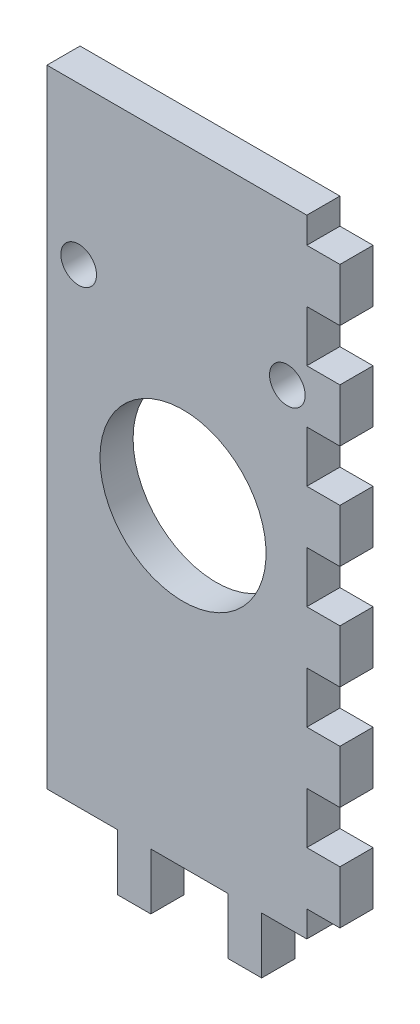
SolidWorks part; units mm, degrees
ref_plane "Front Plane" through (0, 0, 0) normal (0, 0, 1) x (1, 0, 0)
ref_plane "Top Plane" through (0, 0, 0) normal (0, 1, 0) x (1, 0, 0)
ref_plane "Right Plane" through (0, 0, 0) normal (1, 0, 0) x (0, 0, -1)
sketch "Sketch1" plane through (0, 0, 0) normal (0, 1, 0) x (1, 0, 0)
  line L0 (0, 0) -> (-50.5, 0) construction
  line L1 (0, 0) -> (0, 50.5) construction
  line L2 (-50.5, 22.5) -> (-22.5, 22.5)
  line L3 (-22.5, 22.5) -> (-22.5, 50.5)
  line L5 (-22.5, 22.5) -> (-50.5, 22.5)
  line L6 (-22.5, 22.5) -> (-22.5, 25.675)
  line L7 (-22.5, 25.675) -> (-50.5, 25.675)
  line L8 (-50.5, 22.5) -> (-50.5, 25.675)
  line L9 (-22.5, 22.5) -> (-25.675, 22.5)
  line L10 (-22.5, 22.5) -> (-22.5, 50.5)
  line L11 (-22.5, 50.5) -> (-25.675, 50.5)
  line L12 (-25.675, 22.5) -> (-25.675, 50.5)
  point P7 (-37.5, 22.5)
  point P8 (-22.5, 37.5)
  dimension "D1" = 50.5
  dimension "D2" = 50.5
  dimension "D3" = 22.5
  dimension "D4" = 22.5
  dimension "D5" = 37.5
  dimension "D6" = 37.5
  dimension "D7" = 28
  dimension "D8" = 28
  dimension "D9" = 3.175
  dimension "D10" = 3.175
extrude "Boss-Extrude1" add sketch "Sketch1" along normal blind 60 contours L2 L12 L7 L8 | L12 L5 L3 L7 | L12 L7 L3 L11
sketch "Sketch2" plane through (0, 0, -22.5) normal (0, 0, 1) x (1, 0, 0)
  line L0 (-50.5, 30) -> (-22.5, 30) construction
  line L1 (-50.5, 60) -> (-50.5, 0) construction
  line L2 (-22.5, 60) -> (-22.5, 0) construction
  line L3 (-37.5, 60) -> (-37.5, 0) construction
  line L4 (-50.5, 60) -> (-22.5, 60) construction
  line L5 (-50.5, 0) -> (-22.5, 0) construction
  line L7 (-50.5, 60) -> (-22.5758, 60)
  line L15 (-33.125, -5.4) -> (-33.125, 0)
  line L16 (-30, -5.4) -> (-33.125, -5.4)
  line L17 (-30, -5.4) -> (-30, 0)
  line L18 (-40.625, -5.4) -> (-40.625, 0)
  line L19 (-43.75, -5.4) -> (-40.625, -5.4)
  line L20 (-43.75, -5.4) -> (-43.75, 0)
  circle A0 centre (-37.5, 30) radius 8
  dimension "D2" = 16
  dimension "D1" = 15
  dimension "D3" = 5.4
  dimension "D4" = 7.5
  dimension "D6" = 3.125
  dimension "D5" = 7.5
sketch "Sketch3" plane through (-22.5, 0, 0) normal (1, 0, 0) x (0, 0, -1)
  line L0 (22.5, 30) -> (50.5, 30) construction
  line L1 (22.5, 60) -> (22.5, 0) construction
  line L2 (50.5, 60) -> (50.5, 0) construction
  line L3 (37.5, 60) -> (37.5, 0) construction
  line L4 (22.5, 60) -> (50.5, 60) construction
  line L5 (22.5, 0) -> (50.5, 0) construction
  circle A0 centre (37.5, 30) radius 8
  dimension "D1" = 16
  dimension "D2" = 15
extrude "Boss-Extrude4" add sketch "Sketch2" against normal blind 3.175
sketch "Sketch4" plane through (0, 0, -22.5) normal (0, 0, 1) x (1, 0, 0)
  line L0 (-50.5, 30) -> (-22.5, 30) construction
  line L1 (-50.5, 60) -> (-50.5, 0) construction
  line L2 (-22.5, 22) -> (-22.5, 38) construction
  line L3 (-37.5, 60) -> (-37.5, 0) construction
  line L4 (-50.5, 60) -> (-22.5, 60) construction
  line L5 (-50.5, 0) -> (-43.75, 0) construction
  line L6 (-22.5, 60) -> (-22.5, 0) construction
  circle A0 centre (-37.5, 30) radius 8
  dimension "D1" = 16
  dimension "D2" = 15
extrude "Cut-Extrude1" cut sketch "Sketch4" against normal blind 3.175
extrude "Cut-Extrude2" cut sketch "Sketch3" against normal blind 3.175
sketch "Sketch5" plane through (-22.5, 0, 0) normal (1, 0, 0) x (0, 0, -1)
  line L0 (22.5, 0) -> (50.5, 0) construction
  line L1 (22.5, 60) -> (50.5, 60)
  line L10 (22.5, 30) -> (50.5, 30) construction
  line L11 (22.5, 60) -> (22.5, 0) construction
  line L12 (50.5, 60) -> (50.5, 0) construction
  line L13 (43.85, -5.4) -> (43.85, 0)
  line L14 (40.675, -5.4) -> (43.85, -5.4)
  line L15 (40.675, -5.4) -> (40.675, 0)
  line L16 (33.175, -5.4) -> (33.175, 0)
  line L17 (30, -5.4) -> (33.175, -5.4)
  line L18 (30, -5.4) -> (30, 0)
  line L19 (30, 0) -> (33.175, 0)
  line L28 (40.675, 0) -> (43.85, 0)
  point P7 (37.5, 30)
  point P8 (-4.2304, -0.8722)
  point P10 (8.5502, 17.2274)
  dimension "D1" = 7.5
  dimension "D2" = 5.4
  dimension "D3" = 3.175
  dimension "D4" = 7.5
extrude "Boss-Extrude5" add sketch "Sketch5" against normal blind 3.175
sketch "Sketch6" plane through (0, 0, -22.5) normal (0, 0, 1) x (1, 0, 0)
  line L0 (-50.5, 45) -> (-22.5, 45) construction
  line L1 (-50.5, 60) -> (-50.5, 0) construction
  line L2 (-22.5, 60) -> (-22.5, 0) construction
  line L3 (-37.5, 60) -> (-37.5, 0) construction
  line L4 (-50.5, 60) -> (-22.5, 60) construction
  line L5 (-40.625, 0) -> (-33.125, 0) construction
  circle A0 centre (-37.5, 30) radius 8 construction
  circle A1 centre (-37.5, 30) radius 8 construction
  circle A2 centre (-47.5, 45) radius 1.75
  circle A3 centre (-27.5, 45) radius 1.75
  dimension "D1" = 15
  dimension "D3" = 3.5
  dimension "D2" = 10
extrude "Cut-Extrude3" cut sketch "Sketch6" against normal blind 10 contours A2 | A3
sketch "Sketch7" plane through (-22.5, 0, 0) normal (1, 0, 0) x (0, 0, -1)
  line L0 (37.5, 60) -> (37.5, 0) construction
  line L1 (22.5, 60) -> (50.5, 60) construction
  line L2 (33.175, 0) -> (40.675, 0) construction
  line L4 (22.5, 60) -> (22.5, 0) construction
  line L5 (22.5, 45) -> (50.5, 45) construction
  line L6 (50.5, 60) -> (50.5, 0) construction
  circle A0 centre (37.5, 30) radius 8 construction
  circle A1 centre (37.5, 30) radius 8 construction
  circle A2 centre (47.5, 45) radius 1.75
  circle A3 centre (27.5, 45) radius 1.75
  dimension "D1" = 15
  dimension "D3" = 3.5
  dimension "D2" = 10
extrude "Cut-Extrude4" cut sketch "Sketch7" against normal blind 10
sketch "Sketch8" plane through (0, 0, -50.5) normal (0, 0, -1) x (-1, 0, 0)
  line L1 (22.5, 60) -> (25.675, 60)
  line L2 (22.5, 60) -> (22.5, -5.4)
  line L3 (22.5, -5.4) -> (25.675, -5.4)
  line L4 (25.675, 60) -> (25.675, -5.4)
extrude "Cut-Extrude6" cut sketch "Sketch8" against normal up to surface (24.825 mm away) up to face at (-37.2792, 8.2, -25.675)
sketch "Sketch9" plane through (0, 0, -25.675) normal (0, 0, -1) x (-1, 0, 0)
  line L0 (22.5, 60) -> (22.5, 0) construction
  line L1 (22.5, 57.5) -> (25.675, 57.5)
  line L2 (22.5, 57.5) -> (22.5, 52.5)
  line L3 (22.5, 52.5) -> (25.675, 52.5)
  line L4 (25.675, 57.5) -> (25.675, 52.5)
  line L5 (25.675, 60) -> (25.675, 0)
  line L6 (22.5, 60) -> (50.5, 60) construction
  line L7 (22.5, 0) -> (30, 0) construction
  line L8 (22.5, 47.5) -> (25.675, 47.5)
  line L9 (22.5, 42.5) -> (25.675, 42.5)
  line L10 (25.675, 47.5) -> (25.675, 42.5)
  line L11 (22.5, 47.5) -> (22.5, 42.5)
  line L12 (22.5, 37.5) -> (25.675, 37.5)
  line L13 (22.5, 32.5) -> (25.675, 32.5)
  line L14 (25.675, 37.5) -> (25.675, 32.5)
  line L15 (22.5, 37.5) -> (22.5, 32.5)
  line L16 (22.5, 27.5) -> (25.675, 27.5)
  line L17 (22.5, 22.5) -> (25.675, 22.5)
  line L18 (25.675, 27.5) -> (25.675, 22.5)
  line L19 (22.5, 27.5) -> (22.5, 22.5)
  line L20 (22.5, 17.5) -> (25.675, 17.5)
  line L21 (22.5, 12.5) -> (25.675, 12.5)
  line L22 (25.675, 17.5) -> (25.675, 12.5)
  line L23 (22.5, 17.5) -> (22.5, 12.5)
  line L24 (22.5, 7.5) -> (25.675, 7.5)
  line L25 (22.5, 2.5) -> (25.675, 2.5)
  line L26 (25.675, 7.5) -> (25.675, 2.5)
  line L27 (22.5, 7.5) -> (22.5, 2.5)
  line M6 (22.5, 0) -> (30, 0)
  line M16 (50.5, 60) -> (22.5, 60)
  line M17 (22.5, 60) -> (22.5, 0)
  dimension "D2" = 5
  dimension "D3" = 2.5
  dimension "D4" = 5
  dimension "D5" = 3.175
  dimension "D1" = 6
extrude "Cut-Extrude8" cut sketch "Sketch9" against normal blind 10 contours L5 L1 M16 M17 | L8 L5 L3 M17 | L12 L5 L9 M17 | L16 L5 L13 M17 | L20 L5 L17 M17 | L24 L5 L21 M17 | L25 L5 M17 M6
sketch "Sketch10" plane through (0, 0, -25.675) normal (0, 0, -1) x (-1, 0, 0)
  line L108 (25.6344, 60.0406) -> (25.6344, 57.5406)
  line L109 (25.6344, 57.5406) -> (22.4594, 57.5406)
  line L110 (22.4594, 57.5406) -> (22.4594, 52.4594)
  line L111 (22.4594, 52.4594) -> (25.6344, 52.4594)
  line L112 (25.6344, 52.4594) -> (25.6344, 47.5406)
  line L113 (25.6344, 47.5406) -> (22.4594, 47.5406)
  line L114 (22.4594, 47.5406) -> (22.4594, 42.4594)
  line L115 (22.4594, 42.4594) -> (25.6344, 42.4594)
  line L116 (25.6344, 42.4594) -> (25.6344, 37.5406)
  line L117 (25.6344, 37.5406) -> (22.4594, 37.5406)
  line L118 (22.4594, 37.5406) -> (22.4594, 32.4594)
  line L119 (22.4594, 32.4594) -> (25.6344, 32.4594)
  line L120 (25.6344, 32.4594) -> (25.6344, 27.5406)
  line L121 (25.6344, 27.5406) -> (22.4594, 27.5406)
  line L122 (22.4594, 27.5406) -> (22.4594, 22.4594)
  line L123 (22.4594, 22.4594) -> (25.6344, 22.4594)
  line L124 (25.6344, 22.4594) -> (25.6344, 17.5406)
  line L125 (25.6344, 17.5406) -> (22.4594, 17.5406)
  line L126 (22.4594, 17.5406) -> (22.4594, 12.4594)
  line L127 (22.4594, 12.4594) -> (25.6344, 12.4594)
  line L128 (25.6344, 12.4594) -> (25.6344, 7.5406)
  line L129 (25.6344, 7.5406) -> (22.4594, 7.5406)
  line L130 (22.4594, 7.5406) -> (22.4594, 2.4594)
  line L131 (22.4594, 2.4594) -> (25.6344, 2.4594)
  line L132 (25.6344, 2.4594) -> (25.6344, -0.0406)
  line L133 (25.6344, -0.0406) -> (29.9594, -0.0406)
  line L134 (29.9594, -0.0406) -> (29.9594, -5.4406)
  line L135 (29.9594, -5.4406) -> (33.1656, -5.4406)
  line L136 (33.1656, -5.4406) -> (33.1656, -0.0406)
  line L137 (33.1656, -0.0406) -> (40.5844, -0.0406)
  line L138 (40.5844, -0.0406) -> (40.5844, -5.4406)
  line L139 (40.5844, -5.4406) -> (43.7906, -5.4406)
  line L140 (43.7906, -5.4406) -> (43.7906, -0.0406)
  line L141 (43.7906, -0.0406) -> (50.5406, -0.0406)
  line L142 (50.5406, -0.0406) -> (50.5406, 60.0406)
  line L143 (50.5406, 60.0406) -> (25.6344, 60.0406)
  line L144 (25.6344, 60.0406) -> (25.6344, 57.5406)
  line L145 (25.6344, 57.5406) -> (22.4594, 57.5406)
  line L146 (22.4594, 57.5406) -> (22.4594, 52.4594)
  line L147 (22.4594, 52.4594) -> (25.6344, 52.4594)
  line L148 (25.6344, 52.4594) -> (25.6344, 47.5406)
  line L149 (25.6344, 47.5406) -> (22.4594, 47.5406)
  line L150 (22.4594, 47.5406) -> (22.4594, 42.4594)
  line L151 (22.4594, 42.4594) -> (25.6344, 42.4594)
  line L152 (25.6344, 42.4594) -> (25.6344, 37.5406)
  line L153 (25.6344, 37.5406) -> (22.4594, 37.5406)
  line L154 (22.4594, 37.5406) -> (22.4594, 32.4594)
  line L155 (22.4594, 32.4594) -> (25.6344, 32.4594)
  line L156 (25.6344, 32.4594) -> (25.6344, 27.5406)
  line L157 (25.6344, 27.5406) -> (22.4594, 27.5406)
  line L158 (22.4594, 27.5406) -> (22.4594, 22.4594)
  line L159 (22.4594, 22.4594) -> (25.6344, 22.4594)
  line L160 (25.6344, 22.4594) -> (25.6344, 17.5406)
  line L161 (25.6344, 17.5406) -> (22.4594, 17.5406)
  line L162 (22.4594, 17.5406) -> (22.4594, 12.4594)
  line L163 (22.4594, 12.4594) -> (25.6344, 12.4594)
  line L164 (25.6344, 12.4594) -> (25.6344, 7.5406)
  line L165 (25.6344, 7.5406) -> (22.4594, 7.5406)
  line L166 (22.4594, 7.5406) -> (22.4594, 2.4594)
  line L167 (22.4594, 2.4594) -> (25.6344, 2.4594)
  line L168 (25.6344, 2.4594) -> (25.6344, -0.0406)
  line L169 (25.6344, -0.0406) -> (29.9594, -0.0406)
  line L170 (29.9594, -0.0406) -> (29.9594, -5.4406)
  line L171 (29.9594, -5.4406) -> (33.1656, -5.4406)
  line L172 (33.1656, -5.4406) -> (33.1656, -0.0406)
  line L173 (33.1656, -0.0406) -> (40.5844, -0.0406)
  line L174 (40.5844, -0.0406) -> (40.5844, -5.4406)
  line L175 (40.5844, -5.4406) -> (43.7906, -5.4406)
  line L176 (43.7906, -5.4406) -> (43.7906, -0.0406)
  line L177 (43.7906, -0.0406) -> (50.5406, -0.0406)
  line L178 (50.5406, -0.0406) -> (50.5406, 60.0406)
  line L179 (50.5406, 60.0406) -> (25.6344, 60.0406)
  circle A2 centre (27.5, 45) radius 1.7094
  circle A4 centre (27.5, 45) radius 1.7094
  circle A8 centre (47.5, 45) radius 1.7094
  circle A10 centre (47.5, 45) radius 1.7094
  circle A11 centre (37.5, 30) radius 7.9594
  circle A12 centre (37.5, 30) radius 7.9594
  dimension "D1" = 0.0406
  dimension "D2" = 0.0406
  dimension "D3" = 0.0406
  dimension "D4" = 0.0406
extrude "Boss-Extrude6" add sketch "Sketch10" against normal up to surface (3.175 mm away) up to face at (-45.75, 45, -22.5)
equation "\"wall width\"=5.05"
equation "\"D1@Sketch1\"=\"wall width\""
equation "\"D2@Sketch1\"=\"wall width\""
equation "\"belt traveling width\"=2.25"
equation "\"D3@Sketch1\"=\"belt traveling width\""
equation "\"D4@Sketch1\"=\"belt traveling width\""
equation "\"bearing center\"=3.75"
equation "\"D5@Sketch1\"=\"bearing center\""
equation "\"D6@Sketch1\"=\"bearing center\""
equation "\"bearing holder wall width\"=2.8"
equation "\"D7@Sketch1\"=\"bearing holder wall width\""
equation "\"D8@Sketch1\"=\"bearing holder wall width\""
equation "\"wall thickness\"=0.3175"
equation "\"D9@Sketch1\"=\"wall thickness\""
equation "\"D10@Sketch1\"=\"wall thickness\""
equation "\"off wall bearing distance\"=1.5"
equation "\"D1@Sketch2\"=\"off wall bearing distance\""
equation "\"bearing diameter\"=1.6"
equation "\"D2@Sketch2\"=\"bearing diameter\""
equation "\"D1@Sketch3\"=\"bearing diameter\""
equation "\"D2@Sketch3\"=\"off wall bearing distance\""
equation "\"tooth width\"=0.75"
equation "\"D1@Sketch4\"=\"bearing diameter\""
equation "\"D2@Sketch4\"=\"off wall bearing distance\""
equation "\"D5@Sketch9\"=\"wall thickness\""
